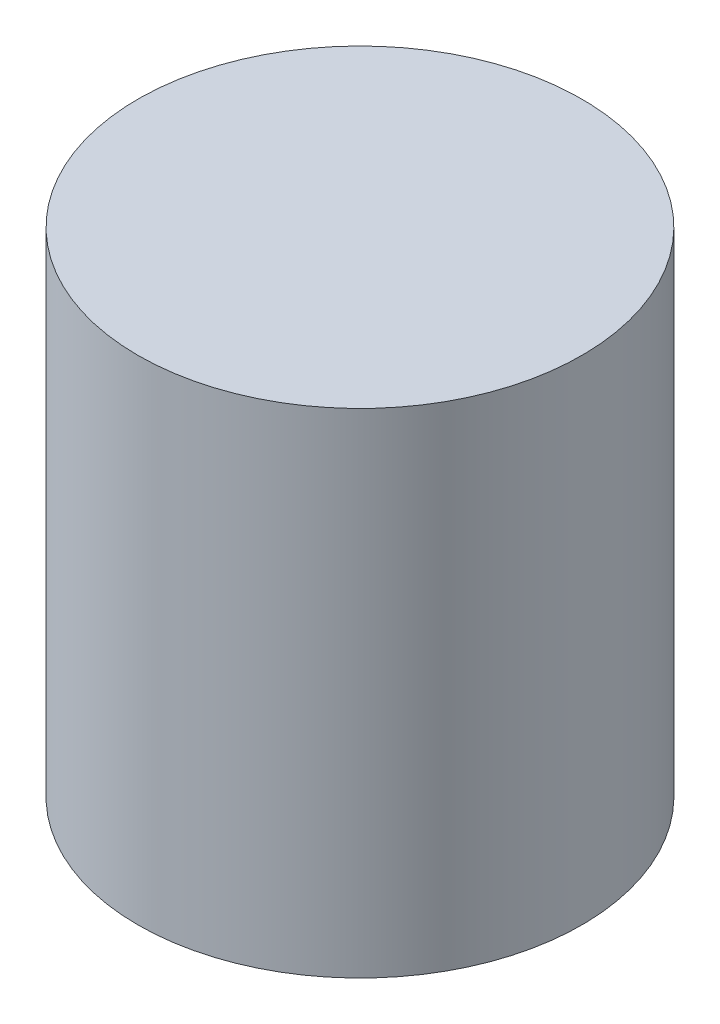
SolidWorks part; units mm, degrees
ref_plane "Front Plane" through (0, 0, 0) normal (0, 0, 1) x (1, 0, 0)
ref_plane "Top Plane" through (0, 0, 0) normal (0, 1, 0) x (1, 0, 0)
ref_plane "Right Plane" through (0, 0, 0) normal (1, 0, 0) x (0, 0, -1)
sketch "Sketch1" plane through (0, 0, 0) normal (0, 1, 0) x (1, 0, 0)
  circle A0 centre (0, 0) radius 45
  dimension "D1" = 90
extrude "Boss-Extrude1" add sketch "Sketch1" along normal blind 100
